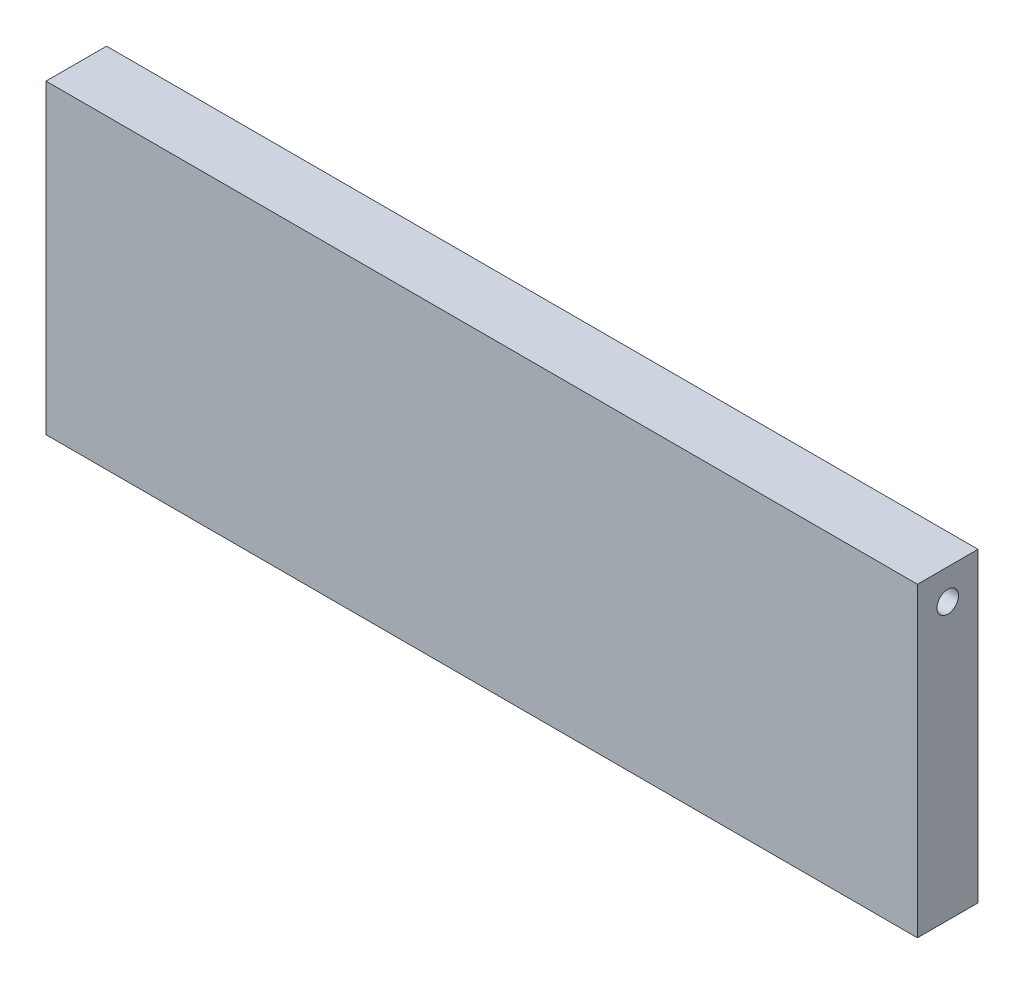
SolidWorks part; units mm, degrees
ref_plane "Front Plane" through (0, 0, 0) normal (0, 0, 1) x (1, 0, 0)
ref_plane "Top Plane" through (0, 0, 0) normal (0, 1, 0) x (1, 0, 0)
ref_plane "Right Plane" through (0, 0, 0) normal (1, 0, 0) x (0, 0, -1)
sketch "Sketch1" plane through (0, 0, 0) normal (0, 1, 0) x (1, 0, 0)
  line L1 (-91.44, -6.35) -> (0, -6.35)
  line L2 (-91.44, -6.35) -> (-91.44, 0)
  line L3 (-91.44, 0) -> (0, 0)
  line L4 (0, -6.35) -> (0, 0)
  point P0 (0, 0)
  dimension "D1" = 6.35
  dimension "D2" = 91.44
extrude "Boss-Extrude1" add sketch "Sketch1" along normal blind 32.131
sketch "Sketch2" plane through (0, 0, 0) normal (1, 0, 0) x (0, 0, -1)
  line L0 (0, 32.131) -> (0, 0) construction
  line L1 (-6.35, 32.131) -> (0, 32.131) construction
  circle A0 centre (-3.175, 28.956) radius 1.1303
  dimension "D3" = 2.2606
  dimension "D1" = 3.175
  dimension "D2" = 3.175
extrude "Cut-Extrude1" cut sketch "Sketch2" against normal blind 12.7
ref_plane "Plane1" through (-45.72, 0, 0) normal (1, 0, 0) x (0, 0, -1)
mirror "Mirror1" about plane through (-45.72, 0, 0) normal (1, 0, 0) of "Cut-Extrude1"
